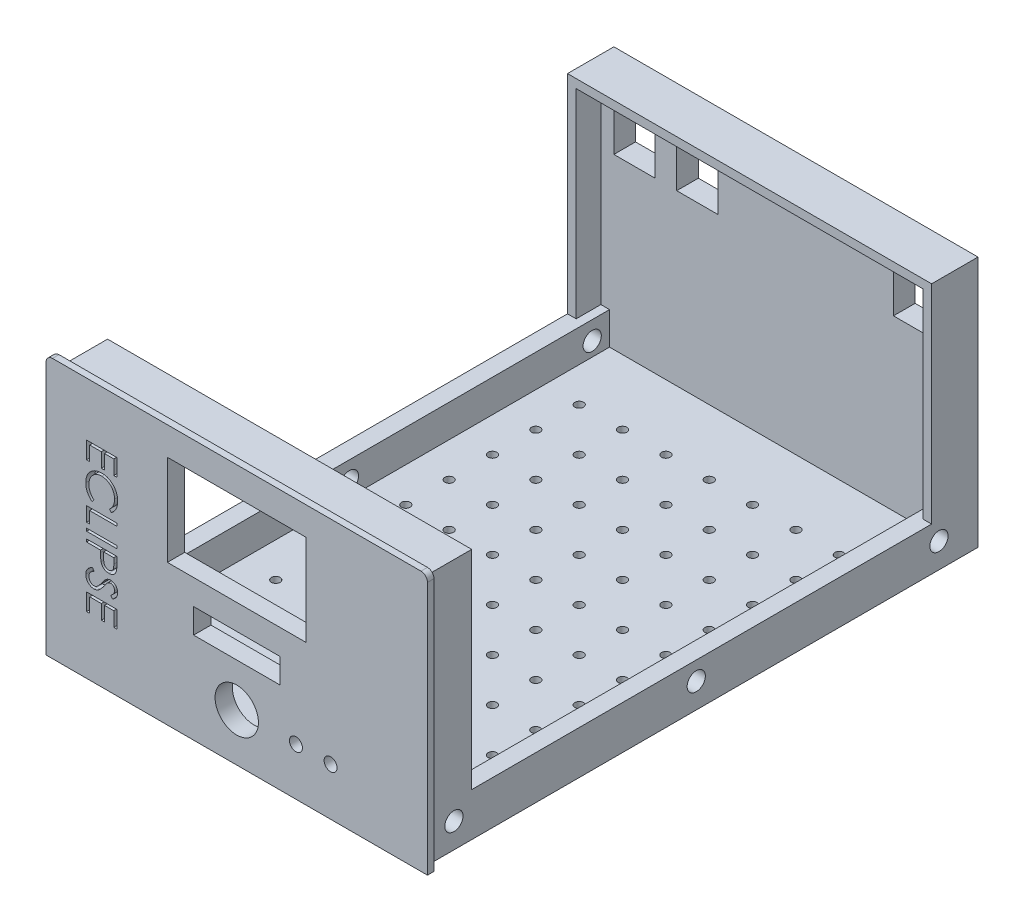
SolidWorks part; units mm, degrees
ref_plane "Front Plane" through (0, 0, 0) normal (0, 0, 1) x (1, 0, 0)
ref_plane "Top Plane" through (0, 0, 0) normal (0, 1, 0) x (1, 0, 0)
ref_plane "Right Plane" through (0, 0, 0) normal (1, 0, 0) x (0, 0, -1)
sketch "Sketch1" plane through (0, 0, 0) normal (0, 0, 1) x (1, 0, 0)
  line L1 (44, -30) -> (-44, -30)
  line L2 (44, -30) -> (44, 30)
  line L3 (44, 30) -> (-44, 30)
  line L4 (-44, -30) -> (-44, 30)
  line L5 (44, -30) -> (-44, 30) construction
  line L6 (44, 30) -> (-44, -30) construction
  point P0 (0, 0)
  dimension "D1" = 88
  dimension "D2" = 60
extrude "Boss-Extrude1" add sketch "Sketch1" against normal blind 1.5
sketch "Sketch3" plane through (0, 0, -1.5) normal (0, 0, -1) x (-1, 0, 0)
  line L4 (44, -30) -> (-44, -30) construction
  line L5 (42, 28) -> (-42, 28)
  line L6 (42, 28) -> (42, -30)
  line L7 (42, -30) -> (-42, -30)
  line L16 (-42, 28) -> (-42, -30)
  line L17 (-44, -30) -> (-44, 30) construction
  line L18 (44, 30) -> (44, -30) construction
  line L19 (-44, 30) -> (44, 30) construction
  dimension "D1" = 0
  dimension "D2" = 2
  dimension "D3" = 2
  dimension "D4" = 2
extrude "Boss-Extrude2" add sketch "Sketch3" along normal blind 127.5
sketch "Sketch8" plane through (42, 0, 0) normal (1, 0, 0) x (0, 0, -1)
  line L0 (1.5, 28) -> (1.5, -30) construction
  line L1 (118.3, -20) -> (12.2, -20)
  line L2 (118.3, -20) -> (118.3, 28)
  line L3 (118.3, 28) -> (12.2, 28)
  line L4 (12.2, -20) -> (12.2, 28)
  line L5 (129, 28) -> (129, -30) construction
  line L6 (129, -30) -> (1.5, -30) construction
  line L7 (129, 28) -> (1.5, 28) construction
  dimension "D1" = 10.7
  dimension "D2" = 10.7
  dimension "D3" = 10
  dimension "D4" = 0
extrude "Cut-Extrude5" cut sketch "Sketch8" against normal through all
sketch "Sketch9" plane through (0, 0, -118.3) normal (0, 0, 1) x (1, 0, 0)
  line L0 (-42, -20) -> (42, -20) construction
  line L1 (-40, 26) -> (40, 26)
  line L2 (-40, 26) -> (-40, -20)
  line L3 (-40, -20) -> (40, -20)
  line L4 (40, 26) -> (40, -20)
  line L5 (-42, 28) -> (42, 28) construction
  line L6 (-42, -20) -> (-42, 28) construction
  line L7 (42, -20) -> (42, 28) construction
  dimension "D1" = 0
  dimension "D2" = 2
  dimension "D3" = 2
  dimension "D4" = 2
extrude "Cut-Extrude6" cut sketch "Sketch9" against normal blind 5.7
sketch "Sketch10" plane through (0, 0, -12.2) normal (0, 0, -1) x (-1, 0, 0)
  line L1 (-40, 26) -> (40, 26)
  line L2 (-40, 26) -> (-40, -20)
  line L3 (-40, -20) -> (40, -20)
  line L4 (40, 26) -> (40, -20)
  line L5 (-42, 28) -> (-42, -20) construction
  line L6 (42, 28) -> (-42, 28) construction
  line L7 (42, 28) -> (42, -20) construction
  line L9 (42, -20) -> (-42, -20) construction
  dimension "D1" = 0
  dimension "D2" = 2
  dimension "D3" = 2
  dimension "D4" = 2
extrude "Cut-Extrude8" cut sketch "Sketch10" against normal blind 8.2
sketch "Sketch17" plane through (0, -20, 0) normal (0, 1, 0) x (1, 0, 0)
  line L0 (-40, 124) -> (40, 124) construction
  line L1 (-38, 124) -> (38, 124)
  line L2 (-38, 124) -> (-38, 4)
  line L3 (-38, 4) -> (38, 4)
  line L4 (38, 124) -> (38, 4)
  line L5 (-38, 124) -> (38, 4) construction
  line L6 (-38, 4) -> (38, 124) construction
  line L7 (-42, 12.2) -> (-42, 118.3) construction
  line L8 (42, 12.2) -> (42, 118.3) construction
  line L10 (40, 4) -> (-40, 4) construction
  point P0 (0, 64)
  dimension "D1" = 0
  dimension "D2" = 4
  dimension "D3" = 4
  dimension "D4" = 0
extrude "Cut-Extrude7" cut sketch "Sketch17" against normal blind 7.5
ref_plane "Plane2" through (0, 0, 0) normal (1, 0, 0) x (0, 0, -1)
sketch "Sketch18" plane through (42, 0, 0) normal (1, 0, 0) x (0, 0, -1)
  line L0 (1.5, 28) -> (1.5, -30) construction
  line L1 (129, 28) -> (129, -30) construction
  line L3 (129, -30) -> (1.5, -30) construction
  line L4 (4, -27.5) -> (124, -27.5) construction
  circle A0 centre (8.1, -24.25) radius 2.1
  circle A1 centre (64, -24.25) radius 2.1
  circle A2 centre (120, -24.25) radius 2.1
  dimension "D1" = 4.2
  dimension "D2" = 9
  dimension "D5" = 4.2
  dimension "D6" = 4.2
  dimension "D3" = 6.6
  dimension "D4" = 62.5
  dimension "3.75" = 3.25
  dimension "D7" = 5.75
extrude "Cut-Extrude10" cut sketch "Sketch18" against normal up to next
mirror "Mirror1" about plane through (0, 0, 0) normal (1, 0, 0) of "Cut-Extrude10"
sketch "Sketch20" plane through (0, -30, 0) normal (0, -1, 0) x (1, 0, 0)
  line L0 (-42, -129) -> (-42, -1.5) construction
  line L1 (-38, -4) -> (38, -4) construction
  circle A0 centre (-30, -19) radius 1
  dimension "D1" = 2
  dimension "D2" = 12
  dimension "D3" = 15
extrude "Cut-Extrude11" cut sketch "Sketch20" against normal up to next
pattern_linear "LPattern1" count 10 spacing 10 along (0, 0, -1) count 7 spacing 10 along (1, 0, 0) of "Cut-Extrude11"
sketch "Sketch26" plane through (0, 0, -129) normal (0, 0, -1) x (-1, 0, 0)
  line L0 (42, -30) -> (42, 28) construction
  line L1 (37, 11.5) -> (27.5, 11.5)
  line L2 (37, 11.5) -> (37, 23)
  line L3 (37, 23) -> (27.5, 23)
  line L4 (27.5, 11.5) -> (27.5, 23)
  line L5 (37, 11.5) -> (27.5, 23) construction
  line L6 (37, 23) -> (27.5, 11.5) construction
  line L8 (42, 28) -> (-42, 28) construction
  point P0 (32.25, 17.25)
  dimension "D1" = 9.5
  dimension "D2" = 11.5
  dimension "D4" = 9.75
  dimension "D6" = 10.75
extrude "Cut-Extrude13" cut sketch "Sketch26" against normal up to next
sketch "Sketch28" plane through (0, 0, -129) normal (0, 0, -1) x (-1, 0, 0)
  line L0 (42, 28) -> (-42, 28) construction
  line L1 (-42, 28) -> (-42, -30) construction
  line L2 (42, -30) -> (42, 28) construction
  point P0 (17.75, 17.25)
  point P1 (-32.25, 17.25)
  dimension "D1" = 10.75
  dimension "D2" = 9.75
  dimension "D3" = 10.75
  dimension "D4" = 24.25
pattern_sketch "Sketch-Pattern4" of "Cut-Extrude13" driven by "Sketch28"
sketch "Sketch30" plane through (0, 0, 0) normal (0, 0, 1) x (1, 0, 0)
  line L3 (-38, -27.5) -> (38, -27.5) construction
  circle A0 centre (13.6514, -19) radius 1.5
  circle A1 centre (21.6514, -19) radius 1.5
  dimension "D1" = 3
  dimension "D2" = 3
  dimension "D3" = 8.5
  dimension "D4" = 8
fillet "Fillet1" radius 1.5 2 edges at (44, 30, -0.75) (-44, 30, -0.75)
sketch "Sketch31" plane through (0, 0, -129) normal (0, 0, -1) x (-1, 0, 0)
  text T0 "Input" font "Century Gothic" height 2
extrude "Cut-Extrude15" cut sketch "Sketch31" against normal blind 2
sketch "Sketch32" plane through (0, 0, -129) normal (0, 0, -1) x (-1, 0, 0)
  text T0 "Output" font "Century Gothic" height 2
extrude "Cut-Extrude16" cut sketch "Sketch32" against normal blind 2
sketch "Sketch33" plane through (0, 0, -129) normal (0, 0, -1) x (-1, 0, 0)
  text T0 "12V                   9V" font "Century Gothic" height 1.5
extrude "Cut-Extrude17" cut sketch "Sketch33" against normal blind 2
sketch "Sketch34" plane through (0, 0, 0) normal (0, 0, 1) x (1, 0, 0)
  line L0 (-40, -20) -> (-40, 26) construction
  line L1 (16, 2.5) -> (-16, 2.5)
  line L2 (16, 2.5) -> (16, 23.5)
  line L3 (16, 23.5) -> (-16, 23.5)
  line L4 (-16, 2.5) -> (-16, 23.5)
  line L5 (16, 2.5) -> (-16, 23.5) construction
  line L6 (16, 23.5) -> (-16, 2.5) construction
  line L8 (40, 26) -> (40, -20) construction
  line L10 (42.5, 30) -> (-42.5, 30) construction
  point P0 (0, 13)
  dimension "D1" = 32
  dimension "D2" = 21
  dimension "D3" = 40
  dimension "D4" = 6.5
  dimension "D5" = 40
extrude "Cut-Extrude18" cut sketch "Sketch34" against normal up to next
sketch "Sketch35" plane through (0, 0, 0) normal (0, 0, 1) x (1, 0, 0)
  line L1 (9.95, -9.005) -> (-9.95, -9.005)
  line L2 (9.95, -9.005) -> (9.95, -3.305)
  line L3 (9.95, -3.305) -> (-9.95, -3.305)
  line L4 (-9.95, -9.005) -> (-9.95, -3.305)
  line L5 (9.95, -9.005) -> (-9.95, -3.305) construction
  line L6 (9.95, -3.305) -> (-9.95, -9.005) construction
  line L7 (40, 26) -> (40, -20) construction
  point P0 (0, -6.155)
  dimension "D1" = 19.9
  dimension "D2" = 5.7
  dimension "D3" = 40
extrude "Cut-Extrude19" cut sketch "Sketch35" against normal up to next
sketch "Sketch36" plane through (0, 0, 0) normal (0, 0, 1) x (1, 0, 0)
  line L1 (-38, -27.5) -> (38, -27.5) construction
  line L2 (-38, -27.5) -> (-38, -20) construction
  line L3 (44, -30) -> (44, 28.5) construction
  circle A0 centre (0, -19) radius 5
  point P2 (0, 0)
  dimension "D1" = 10
  dimension "D2" = 44
  dimension "D3" = 8.5
  dimension "D4" = 38
extrude "Cut-Extrude20" cut sketch "Sketch36" against normal up to next
sketch "Sketch37" plane through (0, -27.5, 0) normal (0, 1, 0) x (1, 0, 0)
  line L0 (-38, 4) -> (38, 4) construction
  line L1 (-4, 9) -> (4, 9)
  line L2 (-4, 9) -> (-4, 16)
  line L3 (-4, 16) -> (4, 16)
  line L4 (4, 9) -> (4, 16)
  line L5 (-4, 9) -> (4, 16) construction
  line L6 (-4, 16) -> (4, 9) construction
  line L7 (-38, 124) -> (-38, 4) construction
  point P0 (0, 12.5)
  dimension "D1" = 5
  dimension "D2" = 7
  dimension "D3" = 8
  dimension "D4" = 38
extrude "Boss-Extrude3" add sketch "Sketch37" along normal blind 5
extrude "Cut-Extrude21" cut sketch "Sketch30" against normal up to next
sketch "Sketch41" plane through (0, 0, 0) normal (0, 0, 1) x (1, 0, 0)
  line L0 (-34.6423, 18.514) -> (-34.6423, -12.0932) construction
sketch "Sketch42" plane through (0, 0, 0) normal (0, 0, 1) x (1, 0, 0)
  text T0 "ECLIPSE" font "Century Gothic" height 7
extrude "Cut-Extrude22" cut sketch "Sketch42" against normal blind 2
sketch "Sketch43" plane through (0, -27.5, 0) normal (0, 1, 0) x (1, 0, 0)
  line L0 (4, 16) -> (-4, 16) construction
  line L1 (-4, 16) -> (4, 16)
  line L2 (-4, 16) -> (-4, 17)
  line L3 (-4, 17) -> (4, 17)
  line L4 (4, 16) -> (4, 17)
  line L5 (-4, 16) -> (4, 17) construction
  line L6 (-4, 17) -> (4, 16) construction
  line L7 (4, 9) -> (4, 16) construction
  line L8 (-4, 16) -> (-4, 9) construction
  point P0 (0, 16.5)
  dimension "D1" = 0
  dimension "D2" = 1
  dimension "D3" = 0
  dimension "D4" = 0
extrude "Boss-Extrude4" add sketch "Sketch43" along normal blind 5.5
